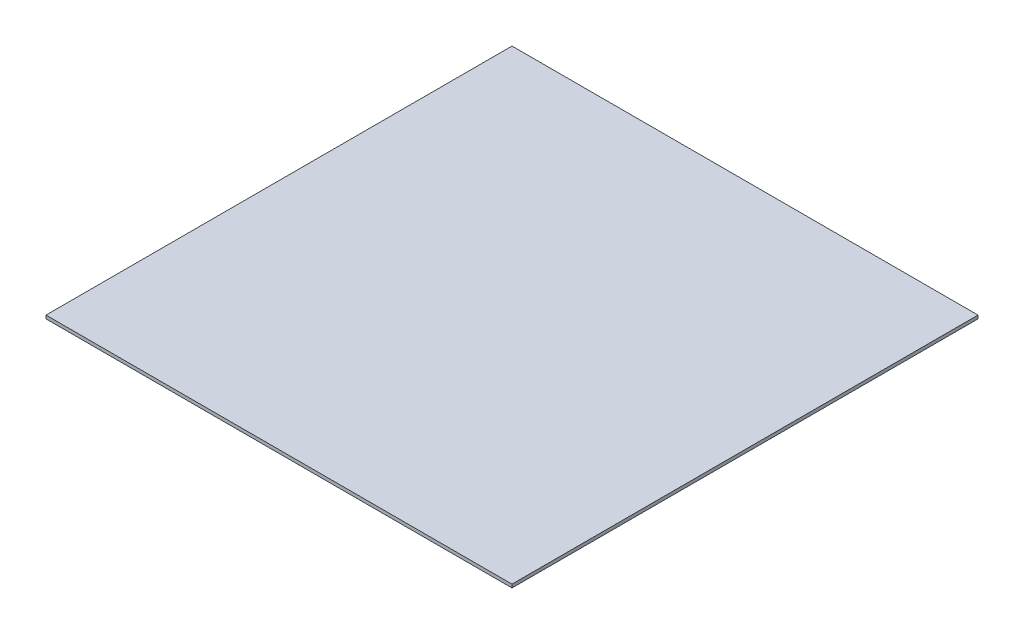
SolidWorks part; units mm, degrees
ref_plane "Front Plane" through (0, 0, 0) normal (0, 0, 1) x (1, 0, 0)
ref_plane "Top Plane" through (0, 0, 0) normal (0, 1, 0) x (1, 0, 0)
ref_plane "Right Plane" through (0, 0, 0) normal (1, 0, 0) x (0, 0, -1)
sketch "Sketch1" plane through (0, 0, 0) normal (0, 1, 0) x (1, 0, 0)
  line L0 (0, 0) -> (107.07, 0)
  line L1 (0, 0) -> (0, 107.07)
  line L2 (0, 107.07) -> (107.07, 107.07)
  line L3 (107.07, 107.07) -> (107.07, 0)
extrude "Boss-Extrude1" add sketch "Sketch1" along normal blind 0.762
